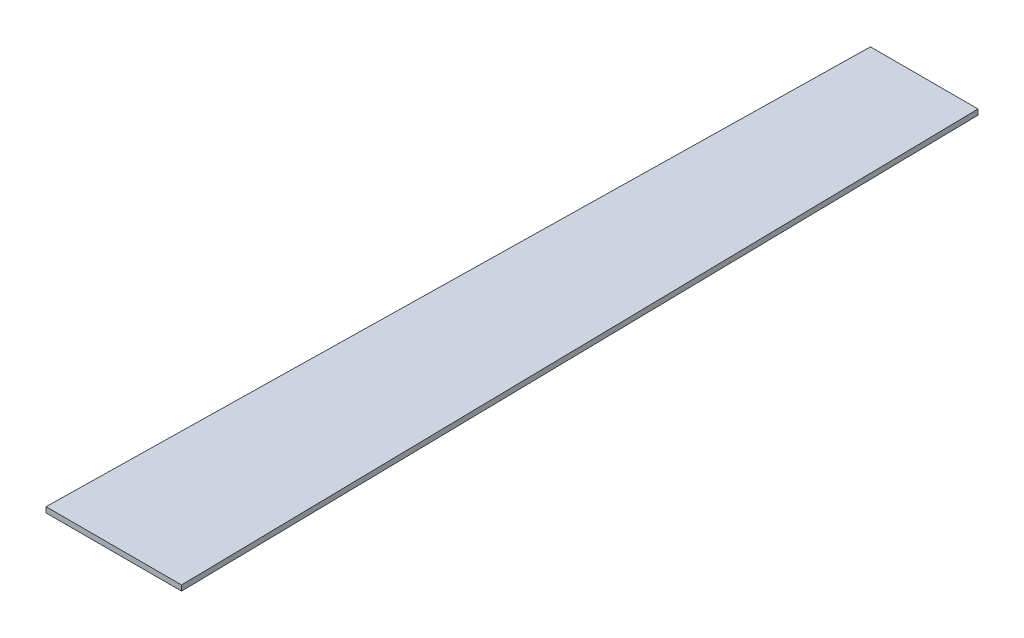
SolidWorks part; units mm, degrees
material "Wrought Stainless Steel"
ref_plane "Front Plane" through (0, 0, 0) normal (0, 0, 1) x (1, 0, 0)
ref_plane "Top Plane" through (0, 0, 0) normal (0, 1, 0) x (1, 0, 0)
ref_plane "Right Plane" through (0, 0, 0) normal (1, 0, 0) x (0, 0, -1)
sketch "Sketch1" plane through (0, 0, 0) normal (0, 1, 0) x (1, 0, 0)
  line L4 (0, 0) -> (2000, 0)
  line L5 (2000, 0) -> (2260, -15067.757)
  line L6 (2260, -15067.757) -> (-260, -15067.757)
  line L7 (0, 0) -> (-260, -15067.757)
  point P3 (1000, 0)
  point P7 (1000, -15067.757)
  dimension "D1" = 2000
  dimension "D2" = 2520
  dimension "D3" = 15070
  dimension "D4" = 15070
extrude "Boss-Extrude1" add sketch "Sketch1" along normal blind 100
sketch "Sketch2" plane through (0, 0, 0) normal (0, -1, 0) x (1, 0, 0)
  line L0 (1000, 15067.757) -> (1000, 13858.8379) construction
  line L1 (-260, 15067.757) -> (2260, 15067.757) construction
  line L6 (125, 14821.8219) -> (1875, 14821.8219)
  line L7 (1875, 14821.8219) -> (1875, 14696.8219)
  line L8 (1875, 14696.8219) -> (125, 14696.8219)
  line L9 (125, 14696.8219) -> (125, 14821.8219)
  point P11 (1000, 14821.8219)
  dimension "D1" = 1750
  dimension "D2" = 125
extrude "Cut-Extrude1" cut sketch "Sketch2" against normal blind 10
pattern_linear "LPattern1" count 30 spacing 500 along (0, 0, -1) of "Cut-Extrude1"
